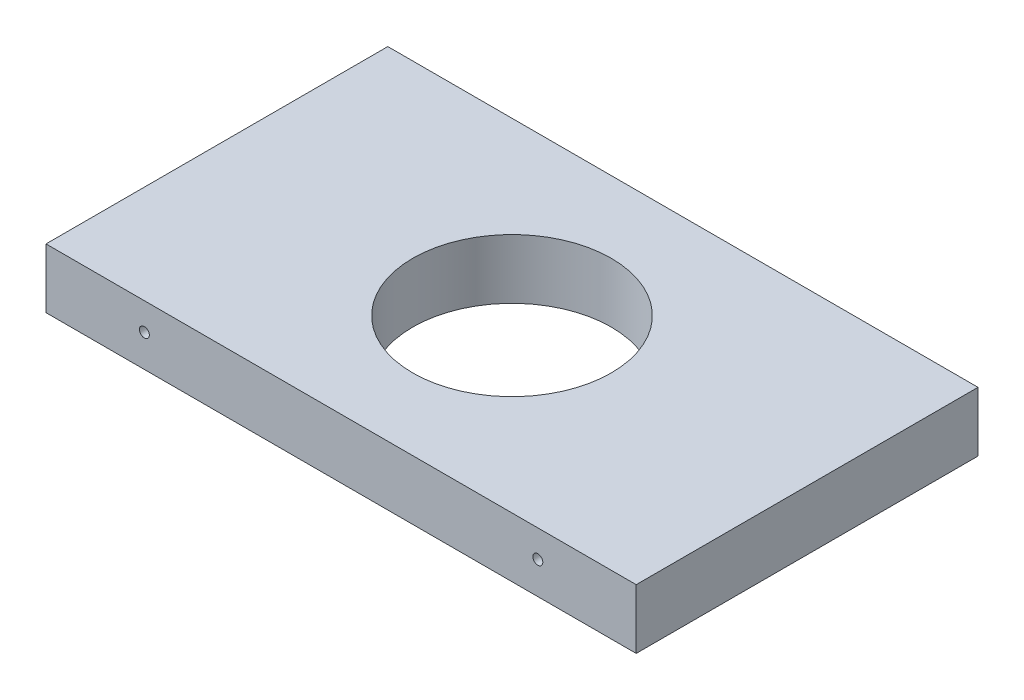
SolidWorks part; units mm, degrees
material "Beech"
ref_plane "Front Plane" through (0, 0, 0) normal (0, 0, 1) x (1, 0, 0)
ref_plane "Top Plane" through (0, 0, 0) normal (0, 1, 0) x (1, 0, 0)
ref_plane "Right Plane" through (0, 0, 0) normal (1, 0, 0) x (0, 0, -1)
sketch "Sketch1" plane through (0, 0, 0) normal (0, 0, 1) x (1, 0, 0)
  line L0 (-322.2545, -292.3211) -> (-133.5295, -292.3211) construction
  line L1 (-322.2545, -431.1858) -> (-322.2545, 0) construction
  line L2 (-133.5295, -157.3) -> (-133.5295, -431.1858) construction
  line L3 (8.6955, -157.3) -> (-256.7045, -157.3) construction
  line L4 (93.2955, -427.3421) -> (-341.3045, -427.3421) construction
  line L5 (-322.2545, -301.8461) -> (-133.5295, -301.8461)
  line L6 (-322.2545, -282.7961) -> (-133.5295, -282.7961)
  line L7 (-322.2545, -301.8461) -> (-322.2545, -282.7961)
  line L8 (-133.5295, -301.8461) -> (-133.5295, -282.7961)
  dimension "D1" = 9.525
  dimension "D2" = 9.525
extrude "Boss-Extrude1" add sketch "Sketch1" along normal up to surface (109.3 mm away)
hole_wizard "Hole1" positions "Sketch2" profile "Sketch3" legacy
sketch "Sketch2" plane through (-124.0045, 10.4243, -12.7) normal (0, 0, -1) x (1, 0, 0)
  line L1 (0, 465.9538) -> (0, 167.7243) construction
  point P1 (113.65, 128.8076)
  point P3 (113.65, 23.941)
  point P5 (-94.6, 161.3743)
  point P7 (94.6, 161.3743)
  point P9 (0, 161.3743)
  point P11 (0, 193.1243)
  point P13 (0, 440.5538)
  point P15 (0, 301.9704)
  point P17 (40.9792, 301.9704)
  point P19 (166.7958, 301.9704)
  point P21 (207.775, 440.5538)
  point P23 (207.775, 333.0214)
  point P25 (207.775, 225.489)
  point P27 (207.775, 137.4243)
  point P29 (207.775, 10.4243)
  point P33 (-207.775, 10.4243)
  point P34 (-207.775, 137.4243)
  point P35 (-207.775, 225.489)
  point P36 (-207.775, 333.0214)
  point P37 (-207.775, 440.5538)
  point P38 (-166.7958, 301.9704)
  point P39 (-40.9792, 301.9704)
  point P40 (-113.65, 23.941)
  point P41 (-113.65, 128.8076)
sketch "Sketch3" plane through (-10.3545, -118.3833, -12.7) normal (1, 0, 0) x (0, 1, 0)
  line L0 (0, 0) -> (0, 32.7039)
  line L1 (0, 32.7039) -> (1.5875, 31.75)
  line L2 (1.5875, 31.75) -> (1.5875, 4.0177)
  line L3 (1.5875, 4.0177) -> (5.08, 0)
  line L4 (5.08, 0) -> (0, 0)
  line L5 (0, -14.3089) -> (0, 102.4216) construction
  line L6 (0, 32.7039) -> (-1.5875, 31.75) construction
  line L7 (-1.5875, 4.0177) -> (-5.08, 0) construction
  dimension "Diameter" = 3.175
  dimension "Depth" = 31.75
  dimension "C-Sink Diameter" = 10.16
  dimension "C-Sink Angle" = 82
  dimension "Drill Angle" = 118
hole_wizard "Hole2" positions "Sketch4" profile "Sketch5" legacy
sketch "Sketch4" plane through (-124.0045, 10.4243, 122) normal (0, 0, 1) x (-1, 0, 0)
  line L1 (0, 465.9538) -> (0, 167.7243) construction
  point P1 (113.65, 128.8076)
  point P3 (113.65, 23.941)
  point P5 (-94.6, 161.3743)
  point P7 (94.6, 161.3743)
  point P9 (0, 161.3743)
  point P11 (0, 193.1243)
  point P13 (0, 440.5538)
  point P15 (0, 301.9704)
  point P17 (40.9792, 301.9704)
  point P19 (166.7958, 301.9704)
  point P21 (207.775, 440.5538)
  point P23 (207.775, 333.0214)
  point P25 (207.775, 225.489)
  point P27 (207.775, 137.4243)
  point P29 (207.775, 10.4243)
  point P33 (-207.775, 10.4243)
  point P34 (-207.775, 137.4243)
  point P35 (-207.775, 225.489)
  point P36 (-207.775, 333.0214)
  point P37 (-207.775, 440.5538)
  point P38 (-166.7958, 301.9704)
  point P39 (-40.9792, 301.9704)
  point P40 (-113.65, 23.941)
  point P41 (-113.65, 128.8076)
sketch "Sketch5" plane through (-237.6545, -118.3833, 122) normal (1, 0, 0) x (0, -1, 0)
  line L0 (0, 0) -> (0, 32.7039)
  line L1 (0, 32.7039) -> (1.5875, 31.75)
  line L2 (1.5875, 31.75) -> (1.5875, 4.0177)
  line L3 (1.5875, 4.0177) -> (5.08, 0)
  line L4 (5.08, 0) -> (0, 0)
  line L5 (0, -14.3089) -> (0, 102.4216) construction
  line L6 (0, 32.7039) -> (-1.5875, 31.75) construction
  line L7 (-1.5875, 4.0177) -> (-5.08, 0) construction
  dimension "Diameter" = 3.175
  dimension "Depth" = 31.75
  dimension "C-Sink Diameter" = 10.16
  dimension "C-Sink Angle" = 82
  dimension "Drill Angle" = 118
hole_wizard "Hole3" positions "Sketch6" profile "Sketch7" legacy
sketch "Sketch6" plane through (-124.0045, 10.4243, 122) normal (0, 0, 1) x (-1, 0, 0)
  line L12 (0, 0) -> (0, 155.0243) construction
  point P0 (-207.775, 333.0214)
  point P3 (-207.775, 225.489)
  point P6 (-207.775, 137.4243)
  point P9 (-172.1667, 4.0743)
  point P12 (-146.0833, 4.0743)
  point P15 (-94.6, 161.3743)
  point P18 (0, 161.3743)
  point P21 (94.6, 161.3743)
  point P24 (146.0833, 4.0743)
  point P27 (172.1667, 4.0743)
  point P30 (207.775, 137.4243)
  point P33 (207.775, 225.489)
  point P36 (207.775, 333.0214)
  point P39 (166.7958, 301.9704)
  point P42 (40.9792, 301.9704)
  point P45 (-40.9792, 301.9704)
  point P48 (-166.7958, 301.9704)
  point P51 (0, 193.1243)
  point P54 (0, 301.9704)
  point P57 (0, 412.3664)
  point P80 (-126.35, 106.8243)
  point P82 (-126.35, 58.6243)
  point P96 (126.35, 58.6243)
  point P97 (126.35, 106.8243)
sketch "Sketch7" plane through (83.7705, -322.5971, 122) normal (1, 0, 0) x (0, -1, 0)
  line L0 (0, 0) -> (0, 32.7039)
  line L1 (0, 32.7039) -> (1.5875, 31.75)
  line L2 (1.5875, 31.75) -> (1.5875, 4.0177)
  line L3 (1.5875, 4.0177) -> (5.08, 0)
  line L4 (5.08, 0) -> (0, 0)
  line L5 (0, -14.3089) -> (0, 102.4216) construction
  line L6 (0, 32.7039) -> (-1.5875, 31.75) construction
  line L7 (-1.5875, 4.0177) -> (-5.08, 0) construction
  dimension "Diameter" = 3.175
  dimension "Depth" = 31.75
  dimension "C-Sink Diameter" = 10.16
  dimension "C-Sink Angle" = 82
  dimension "Drill Angle" = 118
hole_wizard "Hole4" positions "Sketch8" profile "Sketch9" legacy end condition up to next
sketch "Sketch8" plane through (0, -282.7961, 0) normal (0, 1, 0) x (1, 0, 0)
  line L0 (-227.892, -109.3) -> (-227.892, 0) construction
  line L1 (-133.5295, -109.3) -> (-322.2545, -109.3) construction
  line L3 (-133.5295, 0) -> (-322.2545, 0) construction
  point P9 (-227.892, -54.65)
sketch "Sketch9" plane through (-227.892, -282.7961, 54.65) normal (1, 0, 0) x (0, 0, 1)
  line L0 (0, 0) -> (0, 19.05)
  line L1 (0, 19.05) -> (31.75, 19.05)
  line L2 (31.75, 19.05) -> (31.75, 0)
  line L3 (31.75, 0) -> (0, 0)
  line L4 (0, 110) -> (0, -10) construction
  dimension "Diameter" = 63.5
  dimension "Depth" = 19.05
